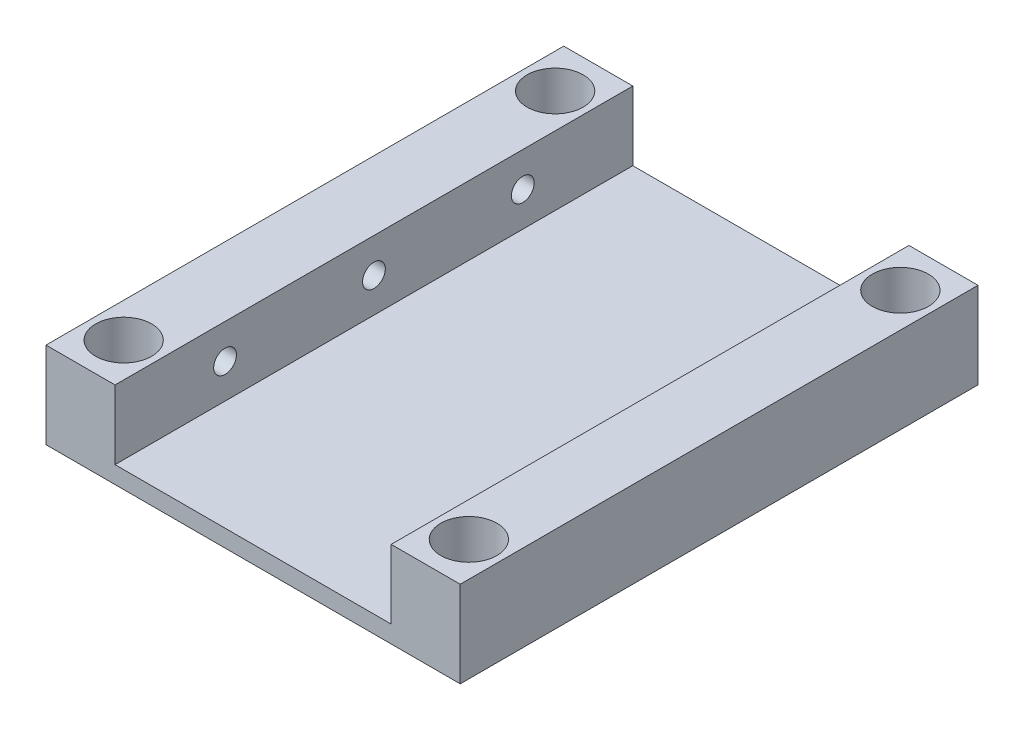
SolidWorks part; units mm, degrees
ref_plane "Front Plane" through (0, 0, 0) normal (0, 0, 1) x (1, 0, 0)
ref_plane "Top Plane" through (0, 0, 0) normal (0, 1, 0) x (1, 0, 0)
ref_plane "Right Plane" through (0, 0, 0) normal (1, 0, 0) x (0, 0, -1)
sketch "Sketch1" plane through (0, 0, 0) normal (0, 0, 1) x (1, 0, 0)
  line L0 (-48, 0) -> (-48, 10)
  line L1 (0, 0) -> (-48, 0)
  line L2 (-48, 10) -> (-40, 10)
  line L3 (-40, 10) -> (-40, 2)
  line L4 (-40, 2) -> (-8, 2)
  line L5 (-8, 2) -> (-8, 10)
  line L6 (-8, 10) -> (0, 10)
  line L7 (0, 10) -> (0, 0)
  dimension "D1" = 32
  dimension "D2" = 8
  dimension "D3" = 8
  dimension "D4" = 10
extrude "Boss-Extrude1" add sketch "Sketch1" along normal blind 60
sketch "Sketch3" plane through (0, 10, 0) normal (0, 1, 0) x (1, 0, 0)
  line L0 (-44, 0) -> (-44, -50000) construction
  line L1 (-40, 0) -> (-48, 0) construction
  line L2 (-4, 0) -> (-4, -50000) construction
  line L3 (0, 0) -> (-8, 0) construction
  line L4 (-64.8967, -5) -> (49935.1033, -5) construction
  line L5 (-66, -55) -> (49934, -55) construction
  line L7 (-40, -60) -> (-48, -60) construction
  circle A0 centre (-44, -5) radius 3.25
  circle A1 centre (-4, -5) radius 3.25
  circle A2 centre (-4, -55) radius 3.25
  circle A3 centre (-44, -55) radius 3.25
  point P4 (-44, 0)
  point P9 (-4, 0)
  dimension "D1" = 6.5
  dimension "D4" = 5
  dimension "D6" = 5
  dimension "D2" = 2
  dimension "D3" = 2
extrude "Cut-Extrude1" cut sketch "Sketch3" against normal blind 8
sketch "Sketch4" plane through (0, 0, 0) normal (0, -1, 0) x (1, 0, 0)
  circle A0 centre (-44, 55) radius 2
  circle A1 centre (-4, 55) radius 2
  circle A2 centre (-4, 5) radius 2
  circle A3 centre (-44, 5) radius 2
  circle A4 centre (-4, 55) radius 3.25 construction
  dimension "D1" = 4
  dimension "D4" = 50
  dimension "D2" = 2
  dimension "D3" = 2
extrude "Cut-Extrude2" cut sketch "Sketch4" against normal blind 8
sketch "Sketch5" plane through (-48, 0, 0) normal (-1, 0, 0) x (0, 0, 1)
  line L0 (1.75, 6) -> (50001.75, 6) construction
  line L1 (51.75, 10) -> (51.75, 2) construction
  line L2 (1.75, 10) -> (1.75, 2) construction
  line L3 (8.25, 2) -> (8.25, 10) construction
  circle A0 centre (12.75, 6) radius 1.32
  circle A1 centre (30, 6) radius 1.32
  circle A2 centre (47.25, 6) radius 1.32
  point P8 (1.75, 6)
  dimension "D1" = 2.64
  dimension "D4" = 4.5
  dimension "D2" = 4.5
  dimension "D3" = 3
extrude "Cut-Extrude3" cut sketch "Sketch5" against normal up to next
sketch "Sketch6" plane through (-48, 0, 0) normal (-1, 0, 0) x (0, 0, 1)
  circle A0 centre (12.75, 6) radius 3.25
  circle A1 centre (30, 6) radius 3.25
  circle A2 centre (47.25, 6) radius 3.25
  circle A3 centre (30, 6) radius 1.32 construction
  dimension "D1" = 6.5
  dimension "D2" = 3
extrude "Cut-Extrude4" cut sketch "Sketch6" against normal blind 6
